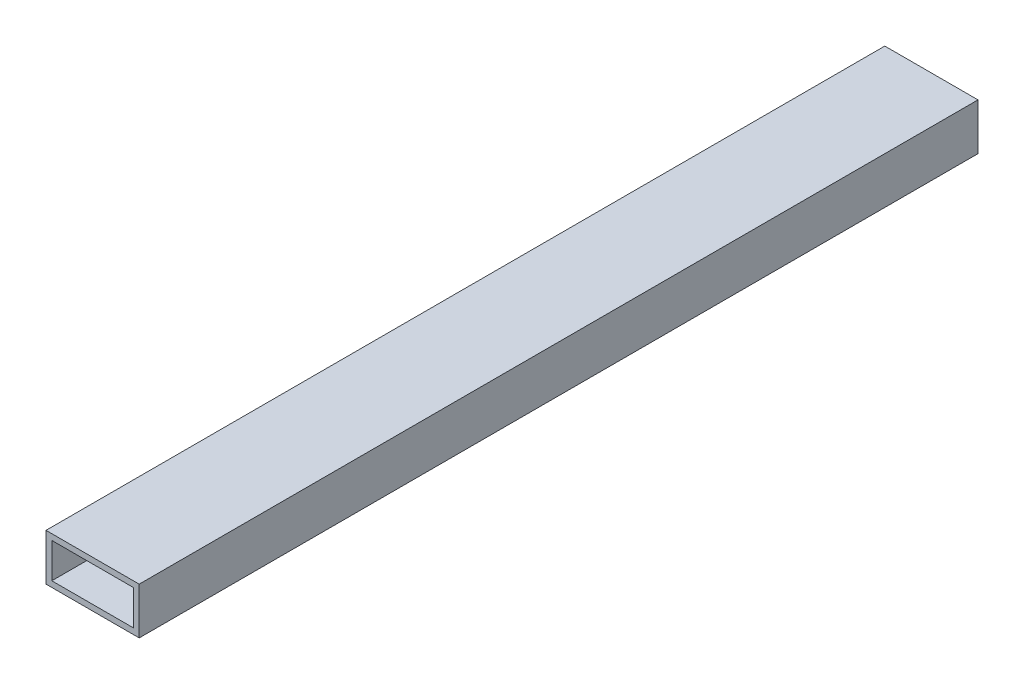
SolidWorks part; units mm, degrees
material "ASTM A36 Steel"
ref_plane "Front Plane" through (0, 0, 0) normal (0, 0, 1) x (1, 0, 0)
ref_plane "Top Plane" through (0, 0, 0) normal (0, 1, 0) x (1, 0, 0)
ref_plane "Right Plane" through (0, 0, 0) normal (1, 0, 0) x (0, 0, -1)
sketch "Sketch1" plane through (0, 0, 0) normal (0, 0, 1) x (1, 0, 0)
  line L1 (-50.8, -25.4) -> (50.8, -25.4)
  line L2 (-50.8, -25.4) -> (-50.8, 25.4)
  line L3 (-50.8, 25.4) -> (50.8, 25.4)
  line L4 (50.8, -25.4) -> (50.8, 25.4)
  line L5 (-50.8, -25.4) -> (50.8, 25.4) construction
  line L6 (-50.8, 25.4) -> (50.8, -25.4) construction
  line L7 (-44.45, -19.05) -> (44.45, -19.05)
  line L8 (-44.45, -19.05) -> (-44.45, 19.05)
  line L9 (-44.45, 19.05) -> (44.45, 19.05)
  line L10 (44.45, -19.05) -> (44.45, 19.05)
  line L11 (-44.45, -19.05) -> (44.45, 19.05) construction
  line L12 (-44.45, 19.05) -> (44.45, -19.05) construction
  point P0 (0, 0)
  point P6 (0, 0)
  dimension "D1" = 6.35
  dimension "D2" = 101.6
  dimension "D3" = 50.8
  dimension "D4" = 6.35
extrude "Boss-Extrude1" add sketch "Sketch1" along normal mid plane 914.4
sketch "Sketch2" plane through (0, 25.4, 0) normal (0, 1, 0) x (1, 0, 0)
  circle A0 centre (0, 0) radius 12.7
  dimension "D1" = 25.4
sketch "Sketch4" plane through (-50.8, 0, 0) normal (-1, 0, 0) x (0, 0, 1)
  line L0 (457.2, -25.4) -> (-457.2, -25.4) construction
  line L1 (12.7, 25.4) -> (-12.7, 25.4)
  line L2 (12.7, 25.4) -> (12.7, -25.4)
  line L3 (12.7, -25.4) -> (-12.7, -25.4)
  line L4 (-12.7, 25.4) -> (-12.7, -25.4)
  line L5 (12.7, 25.4) -> (-12.7, -25.4) construction
  line L6 (12.7, -25.4) -> (-12.7, 25.4) construction
  point P0 (0, 0)
  dimension "D1" = 25.4
extrude "Boss-Extrude3" add sketch "Sketch4" along normal blind 0.0254
equation "\"D4@Sketch1\" = \"D1@Sketch1\""
